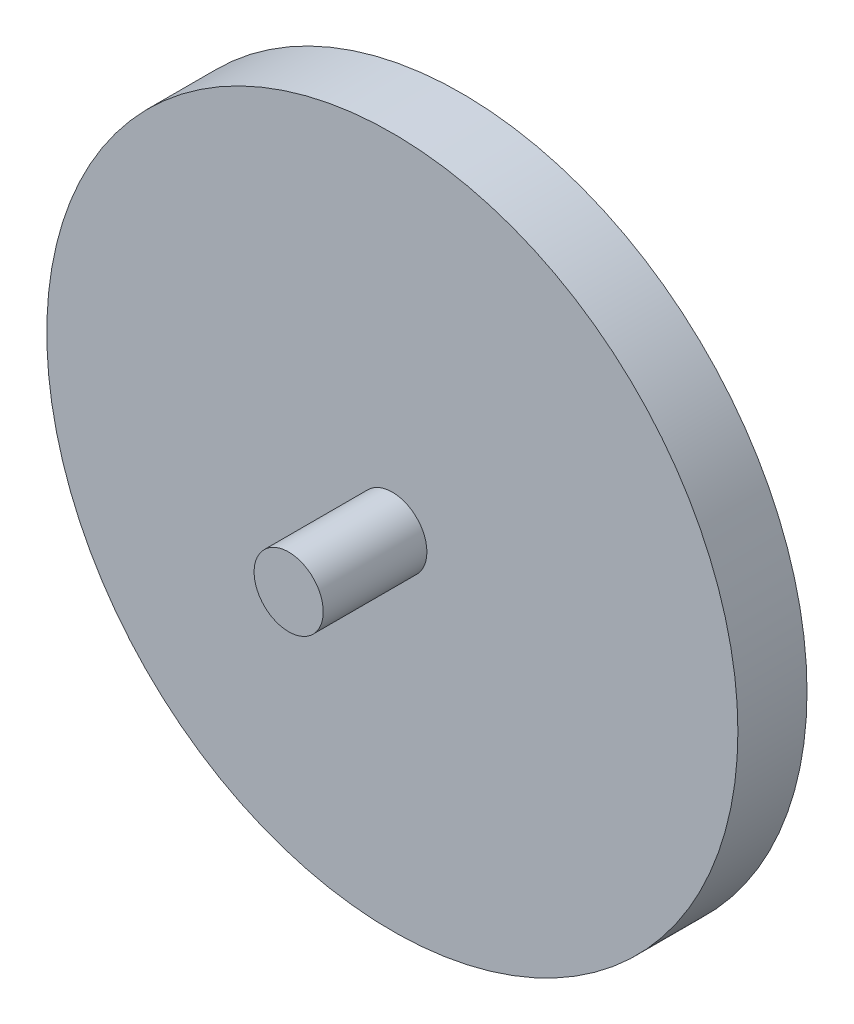
SolidWorks part; units mm, degrees
ref_plane "正面" through (0, 0, 0) normal (0, 0, 1) x (1, 0, 0)
ref_plane "平面" through (0, 0, 0) normal (0, 1, 0) x (1, 0, 0)
ref_plane "右側面" through (0, 0, 0) normal (1, 0, 0) x (0, 0, -1)
sketch "ｽｹｯﾁ1" plane through (0, 0, 0) normal (0, 0, 1) x (1, 0, 0)
  circle A0 centre (-8.0801, 13.9643) radius 10
  dimension "D1" = 20
extrude "ﾎﾞｽ - 押し出し1" add sketch "ｽｹｯﾁ1" along normal blind 2
sketch "ｽｹｯﾁ2" plane through (0, 0, 2) normal (0, 0, 1) x (1, 0, 0)
  circle A0 centre (-8.0801, 13.9643) radius 1
  circle A1 centre (-8.0801, 13.9643) radius 10 construction
  dimension "D1" = 0
extrude "ﾎﾞｽ - 押し出し2" add sketch "ｽｹｯﾁ2" along normal blind 3
